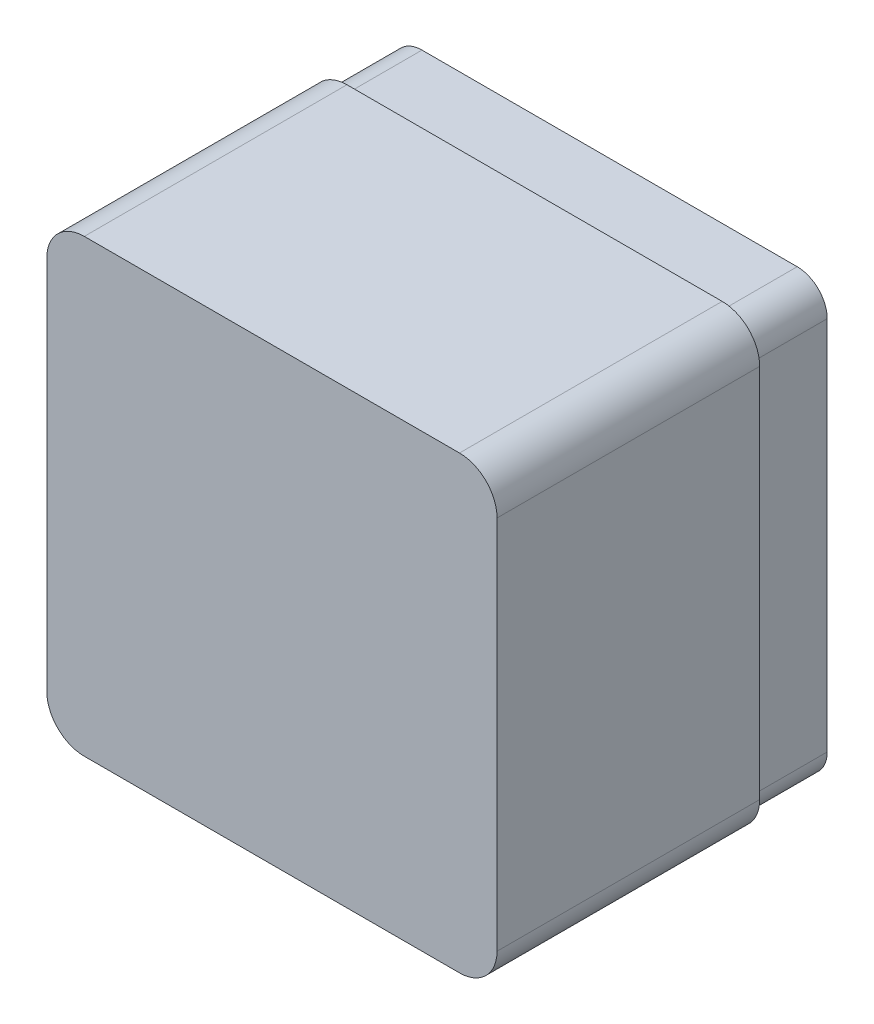
SolidWorks part; units mm, degrees
ref_plane "Front Plane" through (0, 0, 0) normal (0, 0, 1) x (1, 0, 0)
ref_plane "Top Plane" through (0, 0, 0) normal (0, 1, 0) x (1, 0, 0)
ref_plane "Right Plane" through (0, 0, 0) normal (1, 0, 0) x (0, 0, -1)
sketch "Sketch1" plane through (0, 0, 0) normal (0, 0, 1) x (1, 0, 0)
  line L1 (0, 0) -> (120, 0)
  line L2 (0, 0) -> (0, 120)
  line L3 (0, 120) -> (120, 120)
  line L4 (120, 0) -> (120, 120)
  dimension "D1" = 120
  dimension "D2" = 120
extrude "Boss-Extrude1" add sketch "Sketch1" along normal blind 90 contours L3 L4 L1 L2
fillet "Fillet2" radius 10 4 edges at (120, 120, 45) (0, 0, 45) (120, 0, 45) (0, 120, 45)
shell "Shell1" thickness 4
sketch "Sketch2" plane through (0, 0, 0) normal (0, 0, -1) x (-1, 0, 0)
  line L0 (-10, 118) -> (-110, 118)
  line L1 (-118, 110) -> (-118, 10)
  line L2 (-110, 2) -> (-10, 2)
  line L3 (-2, 10) -> (-2, 110)
  line L4 (-10, 120) -> (-110, 120)
  line L5 (-120, 110) -> (-120, 10)
  line L6 (-110, 0) -> (-10, 0)
  line L7 (0, 10) -> (0, 110)
  line L8 (-10, 120) -> (-110, 120)
  line L9 (-120, 110) -> (-120, 10)
  line L10 (-110, 0) -> (-10, 0)
  line L11 (0, 10) -> (0, 110)
  arc A0 (-110, 118) -> (-118, 110) centre (-110, 110) ccw
  arc A1 (-118, 10) -> (-110, 2) centre (-110, 10) ccw
  arc A2 (-10, 2) -> (-2, 10) centre (-10, 10) ccw
  arc A3 (-2, 110) -> (-10, 118) centre (-10, 110) ccw
  arc A4 (-110, 120) -> (-120, 110) centre (-110, 110) ccw
  arc A5 (-120, 10) -> (-110, 0) centre (-110, 10) ccw
  arc A6 (-10, 0) -> (0, 10) centre (-10, 10) ccw
  arc A7 (0, 110) -> (-10, 120) centre (-10, 110) ccw
  arc A8 (-110, 120) -> (-120, 110) centre (-110, 110) ccw
  arc A9 (-120, 10) -> (-110, 0) centre (-110, 10) ccw
  arc A10 (-10, 0) -> (0, 10) centre (-10, 10) ccw
  arc A11 (0, 110) -> (-10, 120) centre (-10, 110) ccw
  dimension "D1" = 0
  dimension "D2" = 2
extrude "Cut-Extrude1" cut sketch "Sketch2" against normal blind 20
